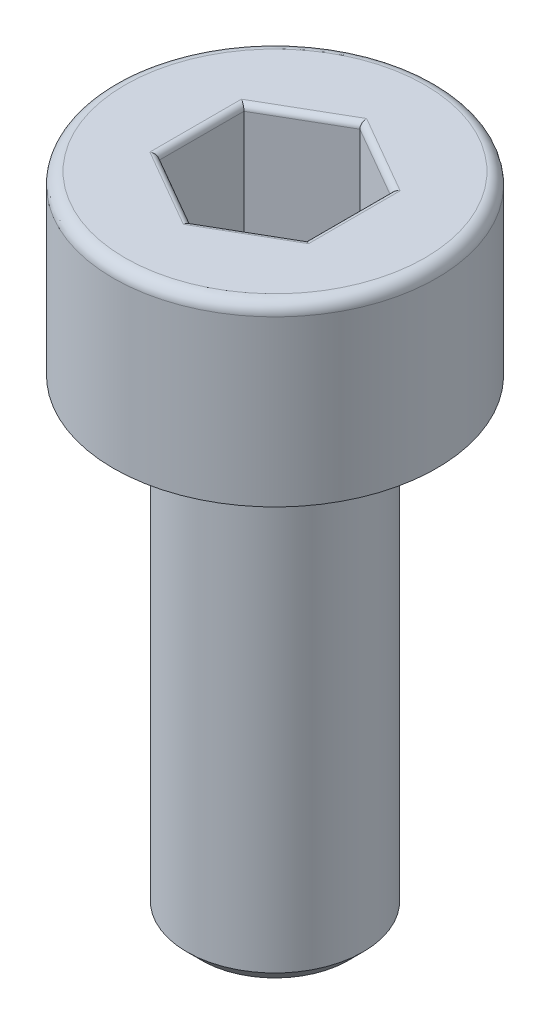
SolidWorks part; units mm, degrees
ref_plane "Front Plane" through (0, 0, 0) normal (0, 0, 1) x (1, 0, 0)
ref_plane "Top Plane" through (0, 0, 0) normal (0, 1, 0) x (1, 0, 0)
ref_plane "Right Plane" through (0, 0, 0) normal (1, 0, 0) x (0, 0, -1)
sketch "Sketch1" plane through (0, 0, 0) normal (0, 0, 1) x (1, 0, 0)
  line L0 (0, 0) -> (0, -47.0967) construction
  line L1 (0, -11) -> (-1.5, -11)
  line L2 (-1.5, -11) -> (-1.5, -3)
  line L3 (-1.5, -3) -> (-2.75, -3)
  line L4 (-2.75, -3) -> (-2.75, 0)
  line L5 (-2.75, 0) -> (0, 0)
  line L6 (0, 0) -> (0, -11)
  dimension "D1" = 8
  dimension "d" = 3
  dimension "k" = 3
  dimension "dk" = 5.5
revolve "Revolve1" add sketch "Sketch1" angle 360 about L0
chamfer "Chamfer1" distance 0.25 angle 45 2 edges at (0, -3, 1.5) (0, -11, 1.5)
fillet "Fillet1" radius 0.2 1 edges at (0, 0, 2.75)
sketch "Sketch2" plane through (0, 0, 0) normal (0, 1, 0) x (1, 0, 0)
  line L1 (0, 1.4434) -> (-1.25, 0.7217)
  line L2 (-1.25, 0.7217) -> (-1.25, -0.7217)
  line L3 (-1.25, -0.7217) -> (0, -1.4434)
  line L4 (0, -1.4434) -> (1.25, -0.7217)
  line L5 (1.25, -0.7217) -> (1.25, 0.7217)
  line L6 (1.25, 0.7217) -> (0, 1.4434)
  circle A0 centre (0, 0) radius 1.25 construction
  dimension "s" = 2.5
extrude "Cut-Extrude1" cut sketch "Sketch2" against normal blind 2
fillet "Fillet2" radius 0.1 12 edges at (-0.625, 0, -1.0825) (-1.25, 0, 0) (-0.625, 0, 1.0825) (0.625, 0, 1.0825) (1.25, 0, 0) (0.625, 0, -1.0825) (1.25, -2, 0) (0.625, -2, 1.0825) (-0.625, -2, 1.0825) (-1.25, -2, 0) (-0.625, -2, -1.0825) (0.625, -2, -1.0825)
